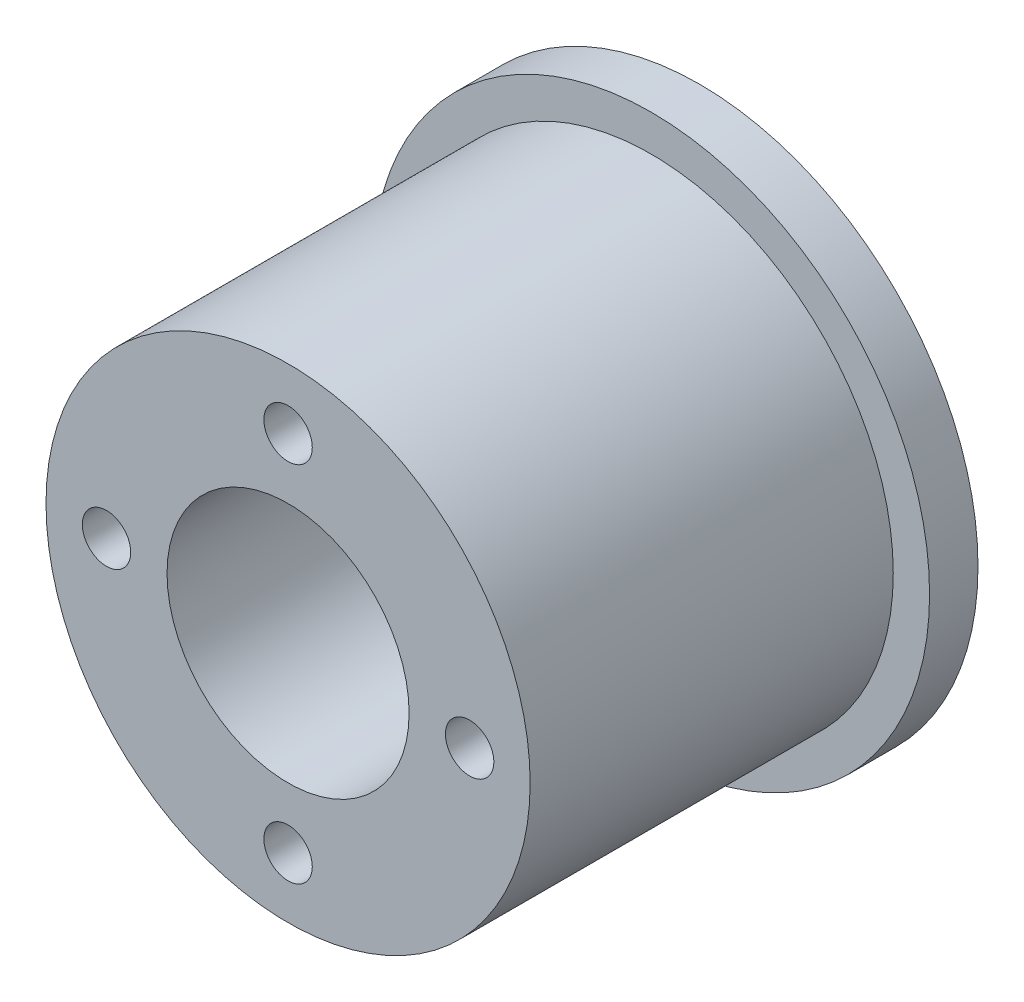
SolidWorks part; units mm, degrees
ref_plane "Front Plane" through (0, 0, 0) normal (0, 0, 1) x (1, 0, 0)
ref_plane "Top Plane" through (0, 0, 0) normal (0, 1, 0) x (1, 0, 0)
ref_plane "Right Plane" through (0, 0, 0) normal (1, 0, 0) x (0, 0, -1)
sketch "Sketch1" plane through (0, 0, 0) normal (0, 0, 1) x (1, 0, 0)
  circle A0 centre (0, 0) radius 23
  circle A1 centre (0, 0) radius 10
  dimension "D1" = 46
  dimension "D2" = 20
extrude "Boss-Extrude1" add sketch "Sketch1" along normal blind 4
sketch "Sketch2" plane through (0, 0, 4) normal (0, 0, 1) x (1, 0, 0)
  circle A0 centre (0, 0) radius 20
  circle A1 centre (0, 0) radius 10 construction
  circle A2 centre (0, 0) radius 10
  circle A3 centre (0, 15) radius 2
  circle A4 centre (15, 0) radius 2
  circle A5 centre (0, -15) radius 2
  circle A6 centre (-15, 0) radius 2
  point P17 (0, 0)
  dimension "D1" = 40
  dimension "D3" = 4
  dimension "D2" = 15
  dimension "D4" = 4
extrude "Boss-Extrude2" add sketch "Sketch2" along normal blind 30
